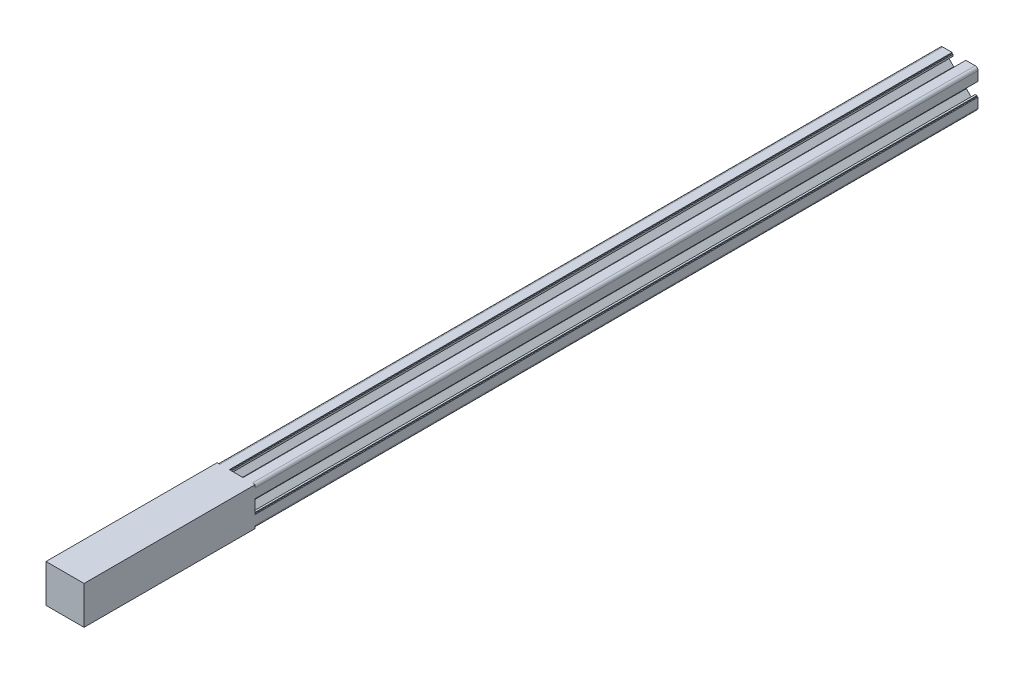
SolidWorks part; units mm, degrees
ref_plane "前视基准面" through (0, 0, 0) normal (0, 0, 1) x (1, 0, 0)
ref_plane "上视基准面" through (0, 0, 0) normal (0, 1, 0) x (1, 0, 0)
ref_plane "右视基准面" through (0, 0, 0) normal (1, 0, 0) x (0, 0, -1)
sketch "草图1" plane through (0, 0, 0) normal (0, 0, 1) x (1, 0, 0)
  line L0 (-3.6, 10) -> (-3.6, 9.5)
  line L1 (-3.6, 9.5) -> (-3.1, 9.5)
  line L2 (-3.1, 9.5) -> (-3.1, 8.5)
  line L3 (-3.1, 8.5) -> (-5.5, 8.5)
  line L4 (-8.5, -10) -> (-3.6, -10)
  line L5 (-10, -8.5) -> (-10, -3.6)
  line L6 (8.5, 10) -> (3.6, 10)
  line L7 (10, 8.5) -> (10, 3.6)
  line L8 (0, 14.8756) -> (0, 0) construction
  line L9 (0, 0) -> (14.1675, 0) construction
  line L10 (-5.5, 8.5) -> (-5.5, 6.65)
  line L11 (-5.5, 6.65) -> (-2.75, 3.9)
  line L12 (-2.75, 3.9) -> (2.75, 3.9)
  line L13 (5.5, 6.65) -> (2.75, 3.9)
  line L14 (5.5, 8.5) -> (5.5, 6.65)
  line L15 (3.1, 8.5) -> (5.5, 8.5)
  line L16 (3.1, 9.5) -> (3.1, 8.5)
  line L17 (3.6, 9.5) -> (3.1, 9.5)
  line L18 (3.6, 10) -> (3.6, 9.5)
  line L19 (-3.6, 10) -> (-8.5, 10)
  line L20 (10, 3.6) -> (9.5, 3.6)
  line L21 (9.5, 3.6) -> (9.5, 3.1)
  line L22 (9.5, 3.1) -> (8.5, 3.1)
  line L23 (8.5, 3.1) -> (8.5, 5.5)
  line L24 (8.5, 5.5) -> (6.65, 5.5)
  line L25 (6.65, 5.5) -> (3.9, 2.75)
  line L26 (3.9, 2.75) -> (3.9, -2.75)
  line L27 (6.65, -5.5) -> (3.9, -2.75)
  line L28 (8.5, -5.5) -> (6.65, -5.5)
  line L29 (8.5, -3.1) -> (8.5, -5.5)
  line L30 (9.5, -3.1) -> (8.5, -3.1)
  line L31 (9.5, -3.6) -> (9.5, -3.1)
  line L32 (10, -3.6) -> (9.5, -3.6)
  line L33 (3.6, -10) -> (3.6, -9.5)
  line L34 (3.6, -9.5) -> (3.1, -9.5)
  line L35 (3.1, -9.5) -> (3.1, -8.5)
  line L36 (3.1, -8.5) -> (5.5, -8.5)
  line L37 (5.5, -8.5) -> (5.5, -6.65)
  line L38 (5.5, -6.65) -> (2.75, -3.9)
  line L39 (2.75, -3.9) -> (-2.75, -3.9)
  line L40 (-5.5, -6.65) -> (-2.75, -3.9)
  line L41 (-5.5, -8.5) -> (-5.5, -6.65)
  line L42 (-3.1, -8.5) -> (-5.5, -8.5)
  line L43 (-3.1, -9.5) -> (-3.1, -8.5)
  line L44 (-3.6, -9.5) -> (-3.1, -9.5)
  line L45 (-3.6, -10) -> (-3.6, -9.5)
  line L46 (-10, -3.6) -> (-9.5, -3.6)
  line L47 (-9.5, -3.6) -> (-9.5, -3.1)
  line L48 (-9.5, -3.1) -> (-8.5, -3.1)
  line L49 (-8.5, -3.1) -> (-8.5, -5.5)
  line L50 (-8.5, -5.5) -> (-6.65, -5.5)
  line L51 (-6.65, -5.5) -> (-3.9, -2.75)
  line L52 (-3.9, -2.75) -> (-3.9, 2.75)
  line L53 (-6.65, 5.5) -> (-3.9, 2.75)
  line L54 (-8.5, 5.5) -> (-6.65, 5.5)
  line L55 (-8.5, 3.1) -> (-8.5, 5.5)
  line L56 (-9.5, 3.1) -> (-8.5, 3.1)
  line L57 (-9.5, 3.6) -> (-9.5, 3.1)
  line L58 (-10, 3.6) -> (-9.5, 3.6)
  line L59 (3.6, -10) -> (8.5, -10)
  line L60 (-10, 3.6) -> (-10, 8.5)
  line L61 (10, -3.6) -> (10, -8.5)
  circle A0 centre (0, 0) radius 2.5
  arc A1 (-10, 8.5) -> (-8.5, 10) centre (-8.5, 8.5) cw
  arc A2 (10, 8.5) -> (8.5, 10) centre (8.5, 8.5) ccw
  arc A3 (-8.5, -10) -> (-10, -8.5) centre (-8.5, -8.5) cw
  arc A4 (8.5, -10) -> (10, -8.5) centre (8.5, -8.5) ccw
  point P0 (-10, 0)
  point P1 (10, 0)
  point P2 (0, 10)
  point P3 (0, -10)
  point P4 (0, 0)
  point P5 (-10, -10)
  point P6 (10, -10)
  point P7 (10, 10)
  point P8 (-10, 10)
  point P13 (0, 0)
  dimension "D1" = 11
  dimension "D2" = 20
  dimension "D3" = 6.2
  dimension "D4" = 7.2
  dimension "D5" = 6.1
  dimension "D6" = 5
  dimension "D7" = 1.5
  dimension "D8" = 45
  dimension "D9" = 0.5
  dimension "D10" = 1
  dimension "D11" = 5.5
extrude "凸台-拉伸1" add sketch "草图1" along normal blind 380
sketch "草图2" plane through (0, 0, 380) normal (0, 0, 1) x (1, 0, 0)
  line L0 (8.5, 10) -> (-8.5, 10)
  line L1 (-10, 8.5) -> (-10, -8.5)
  line L2 (-10, 8.5) -> (-10, 10)
  line L3 (-10, 10) -> (-8.5, 10)
  line L4 (10, 8.5) -> (10, -8.5)
  line L5 (-8.5, -10) -> (8.5, -10)
  line L6 (8.5, -10) -> (10, -10)
  line L7 (10, -10) -> (10, -8.5)
  line L8 (10, 8.5) -> (10, 10)
  line L9 (10, 10) -> (8.5, 10)
  line L10 (-10, -8.5) -> (-10, -10)
  line L11 (-10, -10) -> (-8.5, -10)
extrude "凸台-拉伸2" add sketch "草图2" along normal blind 90
